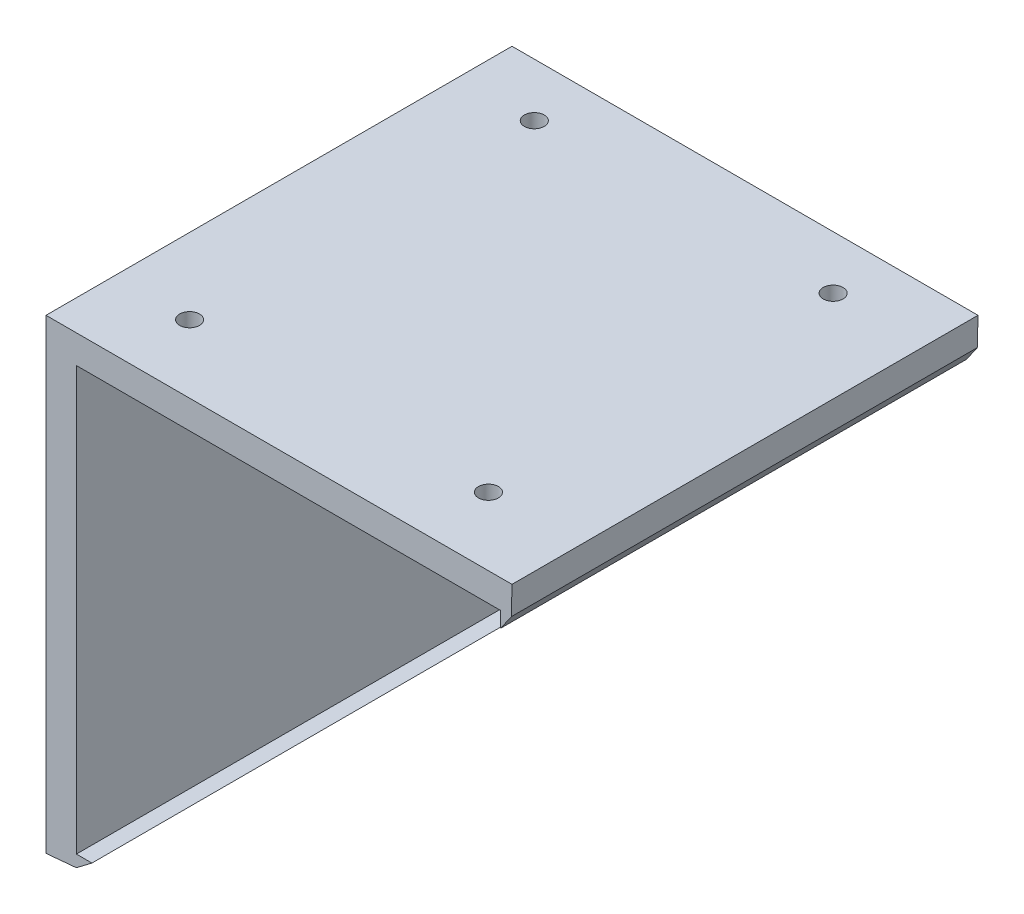
SolidWorks part; units mm, degrees
ref_plane "前视基准面" through (0, 0, 0) normal (0, 0, 1) x (1, 0, 0)
ref_plane "上视基准面" through (0, 0, 0) normal (0, 1, 0) x (1, 0, 0)
ref_plane "右视基准面" through (0, 0, 0) normal (1, 0, 0) x (0, 0, -1)
other "Configuration Table"
sketch "草图1" plane through (0, 0, 0) normal (0, 0, 1) x (1, 0, 0)
  line L2 (28.0418, 1.8227) -> (-1.9582, 1.8227)
  line L3 (-1.9582, 1.8227) -> (-1.9582, -28.1773)
  line L6 (27.3053, 0) -> (27.3053, -1)
  line L7 (0, -27.2371) -> (1, -27.2371)
  line L8 (-1.9582, -28.1773) -> (0, -28)
  line L9 (28.0418, 1.8227) -> (28, 0)
  line L10 (27.3053, -1) -> (28, 0)
  line L11 (0, -28) -> (1, -27.2371)
  line L12 (0, 0) -> (0, -27.2371)
  line L13 (0, 0) -> (27.3053, 0)
  dimension "D1" = 1
  dimension "D2" = 1
  dimension "D3" = 30
  dimension "D4" = 28
  dimension "D5" = 30
  dimension "D6" = 28
extrude "凸台-拉伸1" add sketch "草图1" along normal blind 30
sketch "草图2" plane through (0, 0, 0) normal (0, 1, 0) x (1, 0, 0)
  circle A0 centre (2.9102, -3.4328) radius 0.6407
  circle A1 centre (2.9102, -25.6238) radius 0.6407
  circle A2 centre (22.1479, -3.4328) radius 0.6407
  circle A3 centre (22.1479, -25.6238) radius 0.6407
  point P4 (2.9102, -25.6238)
  point P7 (22.1479, -3.4328)
  point P10 (22.1479, -25.6238)
extrude "切除-拉伸2" cut sketch "草图2" along normal blind 7
